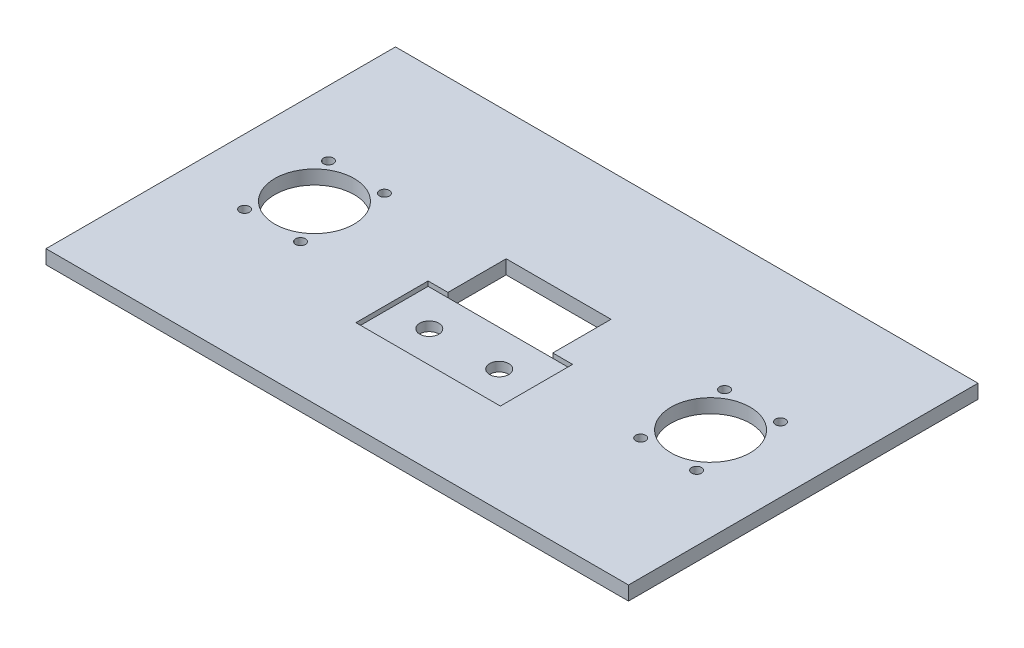
SolidWorks part; units mm, degrees
ref_plane "Front Plane" through (0, 0, 0) normal (0, 0, 1) x (1, 0, 0)
ref_plane "Top Plane" through (0, 0, 0) normal (0, 1, 0) x (1, 0, 0)
ref_plane "Right Plane" through (0, 0, 0) normal (1, 0, 0) x (0, 0, -1)
sketch "Sketch1" plane through (0, 0, 0) normal (0, 1, 0) x (1, 0, 0)
  line L0 (0, -75) -> (0, -20.5)
  line L1 (-125, -75) -> (125, -75)
  line L2 (-125, -75) -> (-125, 75)
  line L3 (-125, 75) -> (125, 75)
  line L4 (125, -75) -> (125, 75)
  line L5 (-125, -75) -> (125, 75) construction
  line L6 (-125, 75) -> (125, -75) construction
  line L7 (-15, -20.5) -> (15, -20.5)
  line L8 (-31, -36) -> (31, -36)
  line L9 (-31, -36) -> (-31, -5)
  line L10 (-31, -5) -> (31, -5)
  line L11 (31, -36) -> (31, -5)
  line L12 (-31, -36) -> (31, -5) construction
  line L13 (-31, -5) -> (31, -36) construction
  circle A0 centre (15, -20.5) radius 4.1
  circle A1 centre (-15, -20.5) radius 4.1
  point P0 (0, 0)
  point P15 (0, -20.5)
  dimension "D8" = 8.2
  dimension "D1" = 250
  dimension "D2" = 150
  dimension "D3" = 54.5
  dimension "D4" = 62
  dimension "D5" = 31
  dimension "D6" = 125
  dimension "D7" = 30
extrude "Boss-Extrude1" add sketch "Sketch1" along normal blind 6
sketch "Sketch2" plane through (0, 6, 0) normal (0, 1, 0) x (1, 0, 0)
  line L0 (-15, -20.5) -> (15, -20.5)
  line L2 (-31, -36) -> (31, -36)
  line L3 (-31, -36) -> (-31, -5)
  line L4 (-31, -5) -> (31, -5)
  line L5 (31, -36) -> (31, -5)
  line L6 (-31, -36) -> (31, -5) construction
  line L7 (-31, -5) -> (31, -36) construction
  point P4 (0, -20.5)
  dimension "D1" = 31
  dimension "D2" = 62
extrude "Cut-Extrude1" cut sketch "Sketch2" against normal blind 2
sketch "Sketch3" plane through (0, 6, 0) normal (0, 1, 0) x (1, 0, 0)
  line L0 (0, -5) -> (0, 7.5)
  line L1 (-31, -5) -> (31, -5) construction
  line L2 (-31, -5) -> (31, -5) construction
  line L3 (-22.5, 20) -> (22.5, 20)
  line L4 (-22.5, 20) -> (-22.5, -5)
  line L5 (-22.5, -5) -> (22.5, -5)
  line L6 (22.5, 20) -> (22.5, -5)
  line L7 (-22.5, 20) -> (22.5, -5) construction
  line L8 (-22.5, -5) -> (22.5, 20) construction
  line L10 (-97, -17.7776) -> (-73, -17.7776) construction
  line L11 (-97, -17.7776) -> (-97, 18.2224) construction
  line L12 (-97, 18.2224) -> (-73, 18.2224) construction
  line L13 (-73, -17.7776) -> (-73, 18.2224) construction
  line L14 (-97, -17.7776) -> (-73, 18.2224) construction
  line L15 (-97, 18.2224) -> (-73, -17.7776) construction
  line L16 (-97, 0.2224) -> (-85, 0.2224) construction
  line L17 (-85, 0.2224) -> (-85, 18.2224) construction
  circle A0 centre (-85, 0.2224) radius 17
  circle A1 centre (85, 0.2224) radius 17
  circle A2 centre (-97, 18.2224) radius 2.125
  circle A3 centre (-97, -17.7776) radius 2.125
  circle A4 centre (-73, -17.7776) radius 2.125
  circle A5 centre (-73, 18.2224) radius 2.125
  circle A6 centre (73, -17.7776) radius 2.125
  circle A7 centre (97, -17.7776) radius 2.125
  circle A8 centre (97, 18.2224) radius 2.125
  circle A9 centre (73, 18.2224) radius 2.125
  point P14 (0, 0)
  dimension "D2" = 34
  dimension "D3" = 170
  dimension "D6" = 4.25
  dimension "D1" = 45
  dimension "D4" = 24
  dimension "D5" = 36
  dimension "D7" = 85
extrude "Cut-Extrude3" cut sketch "Sketch3" against normal blind 29
